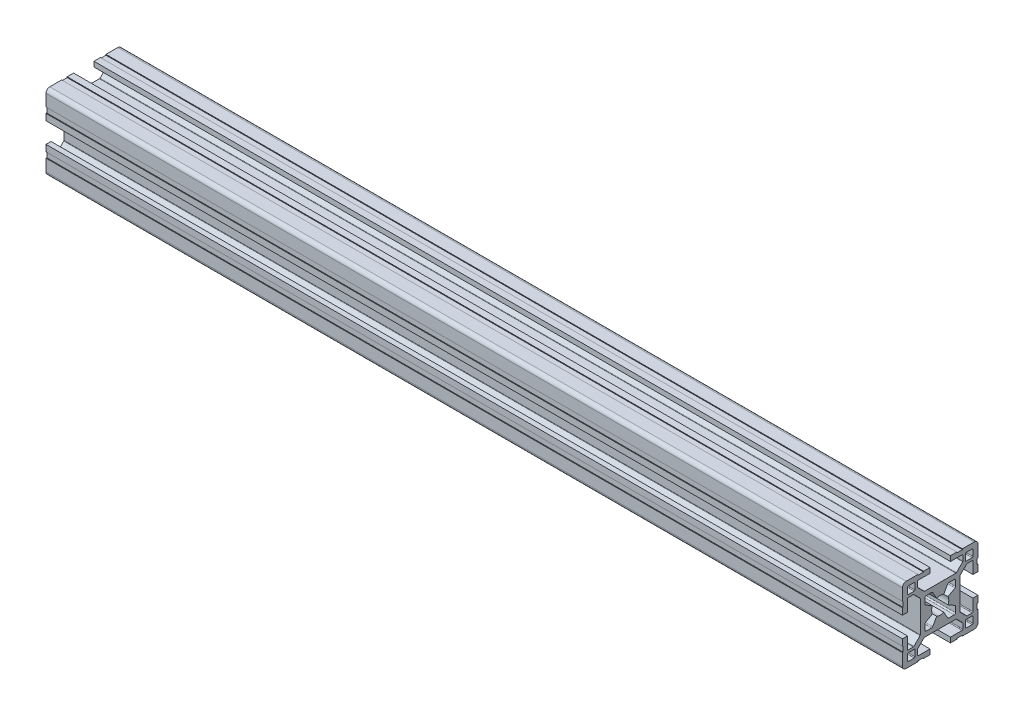
SolidWorks part; units mm, degrees
material "6063-T5"
ref_plane "Plano frontal" through (0, 0, 0) normal (0, 0, 1) x (1, 0, 0)
ref_plane "Plano superior" through (0, 0, 0) normal (0, 1, 0) x (1, 0, 0)
ref_plane "Plano direito" through (0, 0, 0) normal (1, 0, 0) x (0, 0, -1)
sketch "Esboço1" plane through (0, 0, 0) normal (0, 0, 1) x (1, 0, 0)
  line L0 (0, 0) -> (340, 0)
  point P3 (170, 0)
  dimension "D1" = 340
other "Quadrado PF30-11 - PERFIL 3030 CENTRO M8(1)"
ref_plane "Plano1" through (0, 0, 0) normal (1, 0, 0) x (0, 1, 0)
sketch "Sketch1" plane through (0, 0, 0) normal (1, 0, 0) x (0, 1, 0)
  line L0 (-6.1, -3.4254) -> (-6.1, -5.6)
  line L1 (-5.6, -6.1) -> (-3.4254, -6.1)
  line L2 (3.4254, -6.1) -> (5.6, -6.1)
  line L3 (6.1, -5.6) -> (6.1, -3.4254)
  line L4 (6.1, 3.4254) -> (6.1, 5.6)
  line L5 (5.6, 6.1) -> (3.4254, 6.1)
  line L6 (-3.4254, 6.1) -> (-5.6, 6.1)
  line L7 (-6.1, 5.6) -> (-6.1, 3.4254)
  line L8 (15, 6.6) -> (14.7, 6.6)
  line L9 (5.85, -2.9924) -> (3.097, -1.403)
  line L10 (10, 12.7) -> (10, 10.3)
  line L11 (13, -12.7) -> (13, -10.3)
  line L12 (-10.3, -10) -> (-12.7, -10)
  line L13 (-13, 12.7) -> (-13, 10.3)
  line L14 (3.097, 1.403) -> (5.85, 2.9924)
  line L15 (2.9924, 5.85) -> (1.403, 3.097)
  line L16 (-1.403, 3.097) -> (-2.9924, 5.85)
  line L17 (-5.85, 2.9924) -> (-3.097, 1.403)
  line L18 (-3.097, -1.403) -> (-5.85, -2.9924)
  line L19 (-2.9924, -5.85) -> (-1.403, -3.097)
  line L20 (1.403, -3.097) -> (2.9924, -5.85)
  line L21 (10.3, 10) -> (12.7, 10)
  line L22 (13, 10.3) -> (13, 12.7)
  line L23 (12.7, 13) -> (10.3, 13)
  line L24 (12.7, -10) -> (10.3, -10)
  line L25 (10, -10.3) -> (10, -12.7)
  line L26 (10.3, -13) -> (12.7, -13)
  line L27 (-13, -10.3) -> (-13, -12.7)
  line L28 (-12.7, -13) -> (-10.3, -13)
  line L29 (-10, -12.7) -> (-10, -10.3)
  line L30 (-12.7, 10) -> (-10.3, 10)
  line L31 (-10, 10.3) -> (-10, 12.7)
  line L32 (-10.3, 13) -> (-12.7, 13)
  line L33 (15, 4.05) -> (15, 6.6)
  line L34 (13, 4.05) -> (15, 4.05)
  line L35 (13, 8.7) -> (13, 4.05)
  line L36 (10.6799, 9) -> (12.7, 9)
  line L37 (7.9879, 6.4322) -> (10.4678, 8.9121)
  line L38 (7.9, -6.2201) -> (7.9, 6.2201)
  line L39 (10.4678, -8.9121) -> (7.9879, -6.4322)
  line L40 (12.7, -9) -> (10.6799, -9)
  line L41 (13, -4.05) -> (13, -8.7)
  line L42 (15, -4.05) -> (13, -4.05)
  line L43 (15, -6.6) -> (15, -4.05)
  line L44 (14.7, -6.6) -> (15, -6.6)
  line L45 (14.7, -8.8) -> (14.7, -6.6)
  line L46 (15, -8.8) -> (14.7, -8.8)
  line L47 (15, -13.5) -> (15, -8.8)
  line L48 (8.8, -15) -> (13.5, -15)
  line L49 (8.8, -14.7) -> (8.8, -15)
  line L50 (6.6, -14.7) -> (8.8, -14.7)
  line L51 (6.6, -15) -> (6.6, -14.7)
  line L52 (4.05, -15) -> (6.6, -15)
  line L53 (4.05, -13) -> (4.05, -15)
  line L54 (8.7, -13) -> (4.05, -13)
  line L55 (9, -10.6799) -> (9, -12.7)
  line L56 (6.4322, -7.9879) -> (8.9121, -10.4678)
  line L57 (-6.2201, -7.9) -> (6.2201, -7.9)
  line L58 (-8.9121, -10.4678) -> (-6.4322, -7.9879)
  line L59 (-9, -12.7) -> (-9, -10.6799)
  line L60 (-4.05, -13) -> (-8.7, -13)
  line L61 (-4.05, -15) -> (-4.05, -13)
  line L62 (-6.6, -15) -> (-4.05, -15)
  line L63 (-6.6, -14.7) -> (-6.6, -15)
  line L64 (-8.8, -14.7) -> (-6.6, -14.7)
  line L65 (-8.8, -15) -> (-8.8, -14.7)
  line L66 (-13.5, -15) -> (-8.8, -15)
  line L67 (-15, -8.8) -> (-15, -13.5)
  line L68 (-14.7, -8.8) -> (-15, -8.8)
  line L69 (-14.7, -6.6) -> (-14.7, -8.8)
  line L70 (-15, -6.6) -> (-14.7, -6.6)
  line L71 (-15, -4.05) -> (-15, -6.6)
  line L72 (-13, -4.05) -> (-15, -4.05)
  line L73 (-13, -8.7) -> (-13, -4.05)
  line L74 (-10.6799, -9) -> (-12.7, -9)
  line L75 (-7.9879, -6.4322) -> (-10.4678, -8.9121)
  line L76 (-7.9, 6.2201) -> (-7.9, -6.2201)
  line L77 (-10.4678, 8.9121) -> (-7.9879, 6.4322)
  line L78 (-12.7, 9) -> (-10.6799, 9)
  line L79 (-13, 4.05) -> (-13, 8.7)
  line L80 (-15, 4.05) -> (-13, 4.05)
  line L81 (-15, 6.6) -> (-15, 4.05)
  line L82 (-14.7, 6.6) -> (-15, 6.6)
  line L83 (-14.7, 8.8) -> (-14.7, 6.6)
  line L84 (-15, 8.8) -> (-14.7, 8.8)
  line L85 (-15, 13.5) -> (-15, 8.8)
  line L86 (-8.8, 15) -> (-13.5, 15)
  line L87 (-8.8, 14.7) -> (-8.8, 15)
  line L88 (-6.6, 14.7) -> (-8.8, 14.7)
  line L89 (-6.6, 15) -> (-6.6, 14.7)
  line L90 (-4.05, 15) -> (-6.6, 15)
  line L91 (-4.05, 13) -> (-4.05, 15)
  line L92 (-8.7, 13) -> (-4.05, 13)
  line L93 (-9, 10.6799) -> (-9, 12.7)
  line L94 (-6.4322, 7.9879) -> (-8.9121, 10.4678)
  line L95 (6.2201, 7.9) -> (-6.2201, 7.9)
  line L96 (8.9121, 10.4678) -> (6.4322, 7.9879)
  line L97 (9, 12.7) -> (9, 10.6799)
  line L98 (4.05, 13) -> (8.7, 13)
  line L99 (4.05, 15) -> (4.05, 13)
  line L100 (6.6, 15) -> (4.05, 15)
  line L101 (6.6, 14.7) -> (6.6, 15)
  line L102 (8.8, 14.7) -> (6.6, 14.7)
  line L103 (8.8, 15) -> (8.8, 14.7)
  line L104 (13.5, 15) -> (8.8, 15)
  line L105 (15, 8.8) -> (15, 13.5)
  line L106 (14.7, 8.8) -> (15, 8.8)
  line L107 (14.7, 6.6) -> (14.7, 8.8)
  arc A0 (-5.85, -2.9924) -> (-6.1, -3.4254) centre (-5.6, -3.4254) ccw
  arc A1 (-6.1, -5.6) -> (-5.6, -6.1) centre (-5.6, -5.6) ccw
  arc A2 (-3.4254, -6.1) -> (-2.9924, -5.85) centre (-3.4254, -5.6) ccw
  arc A3 (2.9924, -5.85) -> (3.4254, -6.1) centre (3.4254, -5.6) ccw
  arc A4 (5.6, -6.1) -> (6.1, -5.6) centre (5.6, -5.6) ccw
  arc A5 (6.1, -3.4254) -> (5.85, -2.9924) centre (5.6, -3.4254) ccw
  arc A6 (5.85, 2.9924) -> (6.1, 3.4254) centre (5.6, 3.4254) ccw
  arc A7 (6.1, 5.6) -> (5.6, 6.1) centre (5.6, 5.6) ccw
  arc A8 (3.4254, 6.1) -> (2.9924, 5.85) centre (3.4254, 5.6) ccw
  arc A9 (-2.9924, 5.85) -> (-3.4254, 6.1) centre (-3.4254, 5.6) ccw
  arc A10 (-5.6, 6.1) -> (-6.1, 5.6) centre (-5.6, 5.6) ccw
  arc A11 (-6.1, 3.4254) -> (-5.85, 2.9924) centre (-5.6, 3.4254) ccw
  arc A12 (3.097, -1.403) -> (3.097, 1.403) centre (0, 0) ccw
  arc A13 (1.403, 3.097) -> (-1.403, 3.097) centre (0, 0) ccw
  arc A14 (-3.097, 1.403) -> (-3.097, -1.403) centre (0, 0) ccw
  arc A15 (-1.403, -3.097) -> (1.403, -3.097) centre (0, 0) ccw
  arc A16 (10, 10.3) -> (10.3, 10) centre (10.3, 10.3) ccw
  arc A17 (12.7, 10) -> (13, 10.3) centre (12.7, 10.3) ccw
  arc A18 (13, 12.7) -> (12.7, 13) centre (12.7, 12.7) ccw
  arc A19 (10.3, 13) -> (10, 12.7) centre (10.3, 12.7) ccw
  arc A20 (13, -10.3) -> (12.7, -10) centre (12.7, -10.3) ccw
  arc A21 (10.3, -10) -> (10, -10.3) centre (10.3, -10.3) ccw
  arc A22 (10, -12.7) -> (10.3, -13) centre (10.3, -12.7) ccw
  arc A23 (12.7, -13) -> (13, -12.7) centre (12.7, -12.7) ccw
  arc A24 (-12.7, -10) -> (-13, -10.3) centre (-12.7, -10.3) ccw
  arc A25 (-13, -12.7) -> (-12.7, -13) centre (-12.7, -12.7) ccw
  arc A26 (-10.3, -13) -> (-10, -12.7) centre (-10.3, -12.7) ccw
  arc A27 (-10, -10.3) -> (-10.3, -10) centre (-10.3, -10.3) ccw
  arc A28 (-13, 10.3) -> (-12.7, 10) centre (-12.7, 10.3) ccw
  arc A29 (-10.3, 10) -> (-10, 10.3) centre (-10.3, 10.3) ccw
  arc A30 (-10, 12.7) -> (-10.3, 13) centre (-10.3, 12.7) ccw
  arc A31 (-12.7, 13) -> (-13, 12.7) centre (-12.7, 12.7) ccw
  arc A32 (13, 8.7) -> (12.7, 9) centre (12.7, 8.7) ccw
  arc A33 (10.6799, 9) -> (10.4678, 8.9121) centre (10.6799, 8.7) ccw
  arc A34 (7.9879, 6.4322) -> (7.9, 6.2201) centre (8.2, 6.2201) ccw
  arc A35 (7.9, -6.2201) -> (7.9879, -6.4322) centre (8.2, -6.2201) ccw
  arc A36 (10.4678, -8.9121) -> (10.6799, -9) centre (10.6799, -8.7) ccw
  arc A37 (12.7, -9) -> (13, -8.7) centre (12.7, -8.7) ccw
  arc A38 (13.5, -15) -> (15, -13.5) centre (13.5, -13.5) ccw
  arc A39 (8.7, -13) -> (9, -12.7) centre (8.7, -12.7) ccw
  arc A40 (9, -10.6799) -> (8.9121, -10.4678) centre (8.7, -10.6799) ccw
  arc A41 (6.4322, -7.9879) -> (6.2201, -7.9) centre (6.2201, -8.2) ccw
  arc A42 (-6.2201, -7.9) -> (-6.4322, -7.9879) centre (-6.2201, -8.2) ccw
  arc A43 (-8.9121, -10.4678) -> (-9, -10.6799) centre (-8.7, -10.6799) ccw
  arc A44 (-9, -12.7) -> (-8.7, -13) centre (-8.7, -12.7) ccw
  arc A45 (-15, -13.5) -> (-13.5, -15) centre (-13.5, -13.5) ccw
  arc A46 (-13, -8.7) -> (-12.7, -9) centre (-12.7, -8.7) ccw
  arc A47 (-10.6799, -9) -> (-10.4678, -8.9121) centre (-10.6799, -8.7) ccw
  arc A48 (-7.9879, -6.4322) -> (-7.9, -6.2201) centre (-8.2, -6.2201) ccw
  arc A49 (-7.9, 6.2201) -> (-7.9879, 6.4322) centre (-8.2, 6.2201) ccw
  arc A50 (-10.4678, 8.9121) -> (-10.6799, 9) centre (-10.6799, 8.7) ccw
  arc A51 (-12.7, 9) -> (-13, 8.7) centre (-12.7, 8.7) ccw
  arc A52 (-13.5, 15) -> (-15, 13.5) centre (-13.5, 13.5) ccw
  arc A53 (-8.7, 13) -> (-9, 12.7) centre (-8.7, 12.7) ccw
  arc A54 (-9, 10.6799) -> (-8.9121, 10.4678) centre (-8.7, 10.6799) ccw
  arc A55 (-6.4322, 7.9879) -> (-6.2201, 7.9) centre (-6.2201, 8.2) ccw
  arc A56 (6.2201, 7.9) -> (6.4322, 7.9879) centre (6.2201, 8.2) ccw
  arc A57 (8.9121, 10.4678) -> (9, 10.6799) centre (8.7, 10.6799) ccw
  arc A58 (9, 12.7) -> (8.7, 13) centre (8.7, 12.7) ccw
  arc A59 (15, 13.5) -> (13.5, 15) centre (13.5, 13.5) ccw
  point P1 (0, 0)
  point P2 (0, 0)
  point P3 (-15, -15)
  point P4 (0, -15)
  point P5 (-15, 0)
  point P230 (-15, 15)
  point P231 (0, 15)
  point P232 (15, 15)
  point P233 (15, 0)
  point P234 (15, -15)
  point P235 (0, -15)
  point P236 (-15, -15)
  point P237 (-15, 0)
  point P238 (0, 0)
  point P239 (0, 0)
